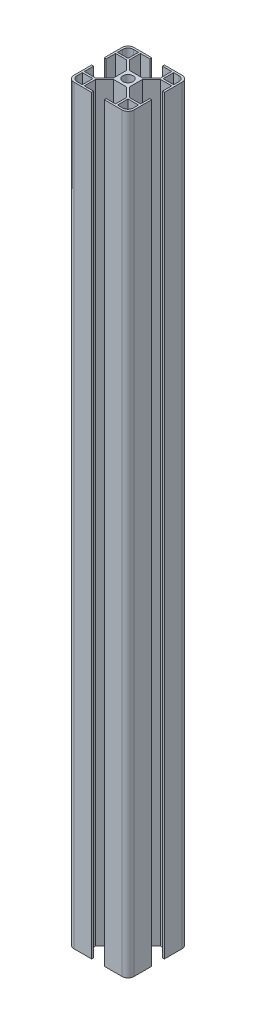
SolidWorks part; units mm, degrees
ref_plane "前视基准面" through (0, 0, 0) normal (0, 0, 1) x (1, 0, 0)
ref_plane "上视基准面" through (0, 0, 0) normal (0, 1, 0) x (1, 0, 0)
ref_plane "右视基准面" through (0, 0, 0) normal (1, 0, 0) x (0, 0, -1)
sketch "草图1" plane through (0, 0, 0) normal (0, 1, 0) x (1, 0, 0)
  line L0 (0, 0) -> (-20, 0) construction
  line L1 (-16.0792, 20) -> (16.0792, 20)
  line L2 (-20, 16.0792) -> (-20, -16.0792)
  line L3 (-16.0792, -20) -> (16.0792, -20)
  line L4 (20, 16.0792) -> (20, -16.0792)
  line L5 (-20, 20) -> (20, -20) construction
  line L6 (-20, -20) -> (20, 20) construction
  line L7 (-5.25, 5.25) -> (5.25, 5.25)
  line L8 (-5.25, 5.25) -> (-5.25, -5.25)
  line L9 (-5.25, -5.25) -> (5.25, -5.25)
  line L10 (5.25, 5.25) -> (5.25, -5.25)
  line L11 (-5.25, 5.25) -> (5.25, -5.25) construction
  line L12 (-5.25, -5.25) -> (5.25, 5.25) construction
  line L17 (-20.658, 20.658) -> (-10.3955, 10.3955) construction
  line L18 (-10.4, 11.3192) -> (-4.3308, 5.25)
  line L19 (-20, 20) -> (-10.4, 20)
  line L20 (-20, 20) -> (-20, 10.4)
  line L21 (-20, 10.4) -> (-10.4, 10.4)
  line L22 (-10.4, 20) -> (-10.4, 10.4)
  line L23 (-20, 20) -> (-10.4, 10.4) construction
  line L24 (-20, 10.4) -> (-10.4, 20) construction
  line L25 (-11.3192, 10.4) -> (-5.25, 4.3308)
  line L26 (-18.7, -11.7) -> (-18.7, -18.7)
  line L27 (-18.7, 11.7) -> (-11.7, 11.7)
  line L28 (-18.7, 11.7) -> (-18.7, 18.7)
  line L29 (-18.7, 18.7) -> (-11.7, 18.7)
  line L30 (-11.7, 11.7) -> (-11.7, 18.7)
  line L31 (-18.7, 11.7) -> (-11.7, 18.7) construction
  line L32 (-18.7, 18.7) -> (-11.7, 11.7) construction
  line L33 (-20, 10.4) -> (-18.7, 10.4)
  line L34 (-20, 10.4) -> (-20, 4.2)
  line L35 (-20, 4.2) -> (-18.7, 4.2)
  line L36 (-18.7, 10.4) -> (-18.7, 4.2)
  line L37 (-18.7, -18.7) -> (-11.7, -18.7)
  line L38 (-11.7, -11.7) -> (-11.7, -18.7)
  line L39 (-18.7, -11.7) -> (-11.7, -11.7)
  line L40 (-20, -4.2) -> (-18.7, -4.2)
  line L41 (-18.7, -10.4) -> (-18.7, -4.2)
  line L42 (-10.4, -11.3192) -> (-4.3308, -5.25)
  line L43 (-11.3192, -10.4) -> (-5.25, -4.3308)
  line L44 (-20, -10.4) -> (-10.4, -10.4)
  line L45 (-10.4, -20) -> (-10.4, -10.4)
  line L46 (0, 20) -> (0, -20) construction
  line L47 (18.7, 18.7) -> (11.7, 18.7)
  line L48 (11.7, 11.7) -> (11.7, 18.7)
  line L49 (18.7, 11.7) -> (11.7, 11.7)
  line L50 (18.7, 11.7) -> (18.7, 18.7)
  line L51 (10.4, 20) -> (10.4, 10.4)
  line L52 (20, 10.4) -> (10.4, 10.4)
  line L53 (20, 4.2) -> (18.7, 4.2)
  line L54 (18.7, 10.4) -> (18.7, 4.2)
  line L55 (10.4, 11.3192) -> (4.3308, 5.25)
  line L56 (11.3192, 10.4) -> (5.25, 4.3308)
  line L57 (11.3192, -10.4) -> (5.25, -4.3308)
  line L58 (10.4, -11.3192) -> (4.3308, -5.25)
  line L59 (18.7, -10.4) -> (18.7, -4.2)
  line L60 (20, -4.2) -> (18.7, -4.2)
  line L61 (20, -10.4) -> (10.4, -10.4)
  line L62 (10.4, -20) -> (10.4, -10.4)
  line L63 (18.7, -11.7) -> (11.7, -11.7)
  line L64 (11.7, -11.7) -> (11.7, -18.7)
  line L65 (18.7, -18.7) -> (11.7, -18.7)
  line L66 (18.7, -11.7) -> (18.7, -18.7)
  line L67 (-4.2, 20) -> (-4.2, 18.7)
  line L68 (-10.4, 18.7) -> (-4.2, 18.7)
  line L69 (-4.2, -20) -> (-4.2, -18.7)
  line L70 (-10.4, -18.7) -> (-4.2, -18.7)
  line L71 (4.2, -20) -> (4.2, -18.7)
  line L72 (10.4, -18.7) -> (4.2, -18.7)
  line L73 (10.4, 18.7) -> (4.2, 18.7)
  line L74 (4.2, 20) -> (4.2, 18.7)
  circle A0 centre (0, 0) radius 3.4
  arc A1 (20, 16.0792) -> (16.0792, 20) centre (16.0792, 16.0792) ccw
  arc A2 (16.0792, -20) -> (20, -16.0792) centre (16.0792, -16.0792) ccw
  arc A3 (-16.0792, -20) -> (-20, -16.0792) centre (-16.0792, -16.0792) cw
  arc A4 (-20, 16.0792) -> (-16.0792, 20) centre (-16.0792, 16.0792) cw
  circle A5 centre (-15.2, 15.2) radius 3.5
  circle A6 centre (-15.2, -15.2) radius 3.5
  circle A7 centre (15.2, 15.2) radius 3.5
  circle A8 centre (15.2, -15.2) radius 3.5
  point P23 (-15.5268, 15.5268)
  point P26 (-15.2, 15.2)
  point P36 (-15.2, 15.2)
  dimension "D1" = 6.8
  dimension "D4" = 3.9208
  dimension "D2" = 40
  dimension "D3" = 40
  dimension "D5" = 14.75
  dimension "D6" = 14.75
  dimension "D7" = 10.4
  dimension "D8" = 0.65
  dimension "D9" = 7
  dimension "D10" = 1.3
  dimension "D11" = 4.2
extrude "凸台-拉伸2" add sketch "草图1" along normal blind 500 contours L70 L45 L3 L69 | A3 L3 L45 L44 L2 L26 L39 L38 L37 | L2 L44 L41 L40 | L37 A6 L26 | L45 L42 L9 L8 L43 L44 | L10 L7 L8 L9 A0 | L58 L62 L61 L57 L10 L9 | L56 L52 L51 L55 L7 L10 | L21 L25 L8 L7 L18 L22 | L3 A2 L4 L61 L62 L63 L66 L65 L64 | A8 L65 L66 | L47 A7 L50 | L4 A1 L1 L51 L52 L50 L49 L48 L47 | A5 L29 L28 | A4 L2 L21 L22 L1 L30 L27 L28 L29 | L22 L68 L67 L1 | L1 L74 L73 L51 | L52 L54 L53 L4 | L36 L21 L2 L35 | L61 L4 L60 L59 | L62 L72 L71 L3
